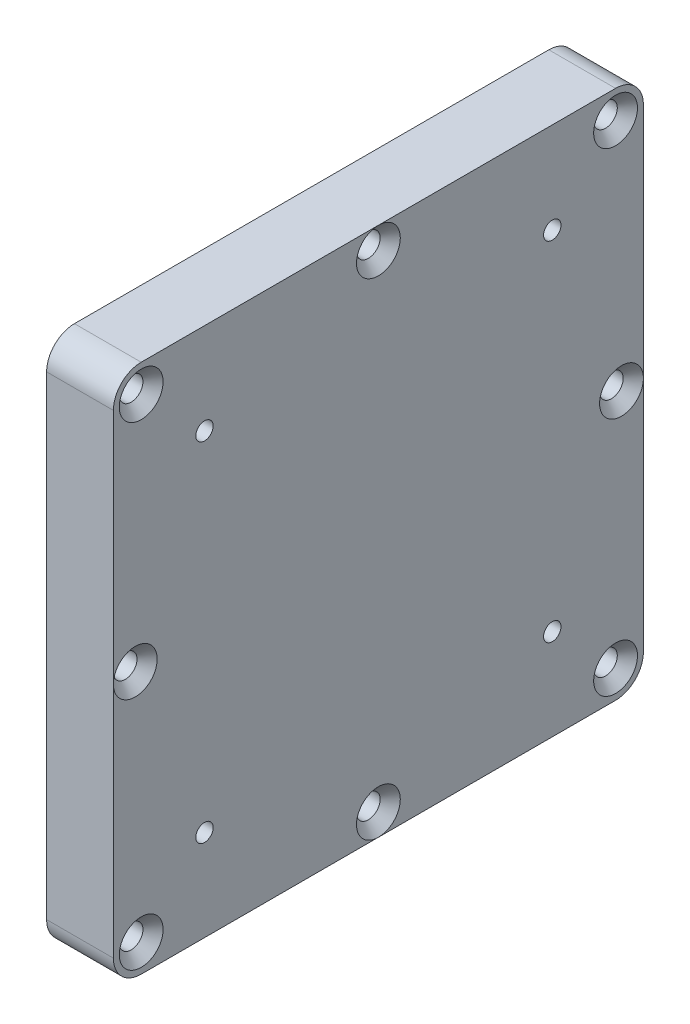
SolidWorks part; units mm, degrees
ref_plane "Front Plane" through (0, 0, 0) normal (0, 0, 1) x (1, 0, 0)
ref_plane "Top Plane" through (0, 0, 0) normal (0, 1, 0) x (1, 0, 0)
ref_plane "Right Plane" through (0, 0, 0) normal (1, 0, 0) x (0, 0, -1)
sketch "Sketch2" plane through (0, 0, 0) normal (1, 0, 0) x (0, 0, -1)
  line L1 (-34.1, -38.1) -> (34.1, -38.1)
  line L2 (-38.1, -34.1) -> (-38.1, 34.1)
  line L3 (-34.1, 38.1) -> (34.1, 38.1)
  line L4 (38.1, -34.1) -> (38.1, 34.1)
  line L5 (-38.1, -38.1) -> (38.1, 38.1) construction
  line L6 (-38.1, 38.1) -> (38.1, -38.1) construction
  arc A0 (-34.1, -38.1) -> (-38.1, -34.1) centre (-34.1, -34.1) cw
  arc A1 (34.1, -38.1) -> (38.1, -34.1) centre (34.1, -34.1) ccw
  arc A2 (34.1, 38.1) -> (38.1, 34.1) centre (34.1, 34.1) cw
  arc A3 (-38.1, 34.1) -> (-34.1, 38.1) centre (-34.1, 34.1) cw
  point P0 (0, 0)
  dimension "D3" = 4
  dimension "D1" = 76.2
  dimension "D2" = 76.2
extrude "Boss-Extrude1" add sketch "Sketch2" along normal blind 9.6
sketch "Sketch21" plane through (9.6, 0, 0) normal (-1, 0, 0) x (0, 0, 1)
  line L0 (-34.1, 34.1) -> (-34.1, -34.1) construction
  line L1 (-34.1, -34.1) -> (34.1, -34.1) construction
  line L2 (-38.1, -34.1) -> (-38.1, 34.1) construction
  line L3 (-34.1, 38.1) -> (34.1, 38.1) construction
  line L4 (38.1, 34.1) -> (38.1, -34.1) construction
  line L5 (34.1, -38.1) -> (-34.1, -38.1) construction
  line L6 (34.1, -34.1) -> (34.1, 34.1) construction
  line L7 (34.1, 34.1) -> (-34.1, 34.1) construction
  dimension "D1" = 4
  dimension "D2" = 4
  dimension "D3" = 4
  dimension "D4" = 4
hole_wizard "CSK for M3 Flat Head Machine Screw1" positions "Sketch22" profile "Sketch23" countersink size "M3" standard "ANSI Metric" end condition through all
sketch "Sketch22" plane through (9.6, 0, 0) normal (-1, 0, 0) x (0, 0, 1)
  line L0 (38.1, 34.1) -> (38.1, -34.1) construction
  line L1 (-38.1, -34.1) -> (-38.1, 34.1) construction
  line L3 (34.1, -38.1) -> (-34.1, -38.1) construction
  line L4 (-34.1, 38.1) -> (34.1, 38.1) construction
  point P0 (-34.1, 34.1)
  point P3 (34.1, 34.1)
  point P6 (34.1, -34.1)
  point P9 (-34.1, -34.1)
  point P12 (0, 34.95)
  point P14 (34.95, 0)
  point P16 (0, -34.95)
  point P18 (-34.95, 0)
  dimension "D1" = 3.15
  dimension "D2" = 3.15
  dimension "D3" = 3.15
  dimension "D4" = 3.15
sketch "Sketch23" plane through (9.6, 34.1, -34.1) normal (0, 1, 0) x (0, 0, -1)
  line L0 (0, 0) -> (0, 9.6)
  line L1 (0, 9.6) -> (1.7, 9.6)
  line L2 (1.7, 9.6) -> (1.7, 1.45)
  line L3 (1.7, 1.45) -> (3.15, 0)
  line L5 (3.15, 0) -> (0, 0)
  line L6 (-1.7, 1.45) -> (-3.15, 0) construction
  line L11 (0, -6.35) -> (0, 107.95) construction
  dimension "Thru Hole Dia." = 3.4
  dimension "Thru Hole Depth" = 9.6
  dimension "Near C'Sink Dia." = 6.3
  dimension "Near C'Sink Angle" = 90
hole_wizard "M3x0.5 Tapped Hole1" positions "Sketch27" profile "Sketch26" tap size "M3x0.5" standard "ANSI Metric"
sketch "Sketch27" plane through (9.6, 0, 0) normal (1, 0, 0) x (0, 0, -1)
  point P0 (-25, 25)
  point P2 (25, 25)
  point P4 (25, -25)
  point P6 (-25, -25)
  dimension "D1" = 50
  dimension "D2" = 25
  dimension "D3" = 25
  dimension "D4" = 25
sketch "Sketch26" plane through (9.6, 25, 25) normal (0, 1, 0) x (0, 0, -1)
  line L0 (0, 0) -> (0, 7.5)
  line L1 (0, 7.5) -> (1.25, 6.7489)
  line L2 (1.25, 6.7489) -> (1.25, 0)
  line L5 (1.25, 0) -> (0, 0)
  line L10 (0, 7.5) -> (-1.25, 6.7489) construction
  line L11 (0, -6.35) -> (0, 107.95) construction
  dimension "Tap Drill Dia." = 2.5
  dimension "Tap Drill Depth" = 7.5
  dimension "Drill Angle" = 118
